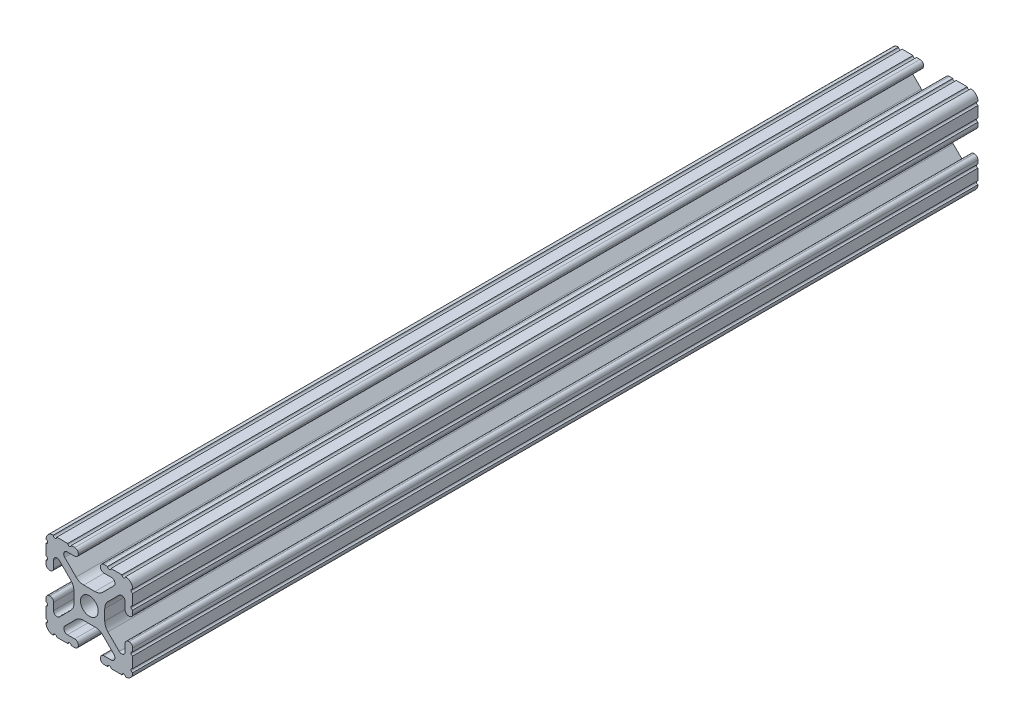
SolidWorks part; units mm, degrees
ref_plane "Front Plane" through (0, 0, 0) normal (0, 0, 1) x (1, 0, 0)
ref_plane "Top Plane" through (0, 0, 0) normal (0, 1, 0) x (1, 0, 0)
ref_plane "Right Plane" through (0, 0, 0) normal (1, 0, 0) x (0, 0, -1)
sketch "Sketch1" plane through (0, 0, 0) normal (0, 0, 1) x (1, 0, 0)
  line L88 (-7.1797, -8.6452) -> (-3.9523, -5.4237)
  line L89 (-1.7093, -4.4958) -> (1.7093, -4.4958)
  line L90 (3.9523, -5.4237) -> (7.1797, -8.6452)
  line L91 (6.4164, -10.4902) -> (4.2875, -10.4902)
  line L92 (3.2385, -11.5392) -> (3.2385, -11.651)
  line L93 (4.2875, -12.7) -> (5.3171, -12.7)
  line L94 (6.3331, -12.7) -> (9.5504, -12.7)
  line L95 (12.7, -9.5504) -> (12.7, -6.3331)
  line L96 (12.7, -5.3171) -> (12.7, -4.2875)
  line L97 (11.651, -3.2385) -> (11.5392, -3.2385)
  line L98 (10.4902, -4.2875) -> (10.4902, -6.4021)
  line L99 (8.7371, -7.1294) -> (5.441, -3.8408)
  line L100 (4.5085, -1.5932) -> (4.5085, 1.5932)
  line L101 (5.441, 3.8408) -> (8.7371, 7.1294)
  line L102 (10.4902, 6.4021) -> (10.4902, 4.2875)
  line L103 (11.5392, 3.2385) -> (11.651, 3.2385)
  line L104 (12.7, 4.2875) -> (12.7, 5.3171)
  line L105 (12.7, 6.3331) -> (12.7, 9.5504)
  line L106 (9.5504, 12.7) -> (6.3331, 12.7)
  line L107 (5.3171, 12.7) -> (4.2875, 12.7)
  line L108 (3.2385, 11.651) -> (3.2385, 11.5392)
  line L109 (4.2875, 10.4902) -> (6.4768, 10.4902)
  line L110 (7.207, 8.7244) -> (3.8983, 5.4232)
  line L111 (1.6558, 4.4958) -> (-1.6558, 4.4958)
  line L112 (-3.8983, 5.4232) -> (-7.207, 8.7244)
  line L113 (-6.4768, 10.4902) -> (-4.2875, 10.4902)
  line L114 (-3.2385, 11.5392) -> (-3.2385, 11.651)
  line L115 (-4.2875, 12.7) -> (-5.3171, 12.7)
  line L116 (-6.3331, 12.7) -> (-9.5504, 12.7)
  line L117 (-12.7, 9.5504) -> (-12.7, 6.3331)
  line L118 (-12.7, 5.3171) -> (-12.7, 4.2875)
  line L119 (-11.651, 3.2385) -> (-11.5392, 3.2385)
  line L120 (-10.4902, 4.2875) -> (-10.4902, 6.4021)
  line L121 (-8.7371, 7.1294) -> (-5.441, 3.8408)
  line L122 (-4.5085, 1.5932) -> (-4.5085, -1.5932)
  line L123 (-5.441, -3.8408) -> (-8.7371, -7.1294)
  line L124 (-10.4902, -6.4021) -> (-10.4902, -4.2875)
  line L125 (-11.5392, -3.2385) -> (-11.651, -3.2385)
  line L126 (-12.7, -4.2875) -> (-12.7, -5.3171)
  line L127 (-12.7, -6.3331) -> (-12.7, -9.5504)
  line L128 (-9.5504, -12.7) -> (-6.3331, -12.7)
  line L129 (-5.3171, -12.7) -> (-4.2875, -12.7)
  line L130 (-3.2385, -11.651) -> (-3.2385, -11.5392)
  line L131 (-4.2875, -10.4902) -> (-6.4164, -10.4902)
  circle A1 centre (0, 0) radius 2.6035
  arc A104 (-7.1797, -8.6452) -> (-6.4164, -10.4902) centre (-6.4164, -9.4098) ccw
  arc A105 (-1.7093, -4.4958) -> (-3.9523, -5.4237) centre (-1.7093, -7.6708) ccw
  arc A106 (3.9523, -5.4237) -> (1.7093, -4.4958) centre (1.7093, -7.6708) ccw
  arc A107 (6.4164, -10.4902) -> (7.1797, -8.6452) centre (6.4164, -9.4098) ccw
  arc A108 (4.2875, -10.4902) -> (3.2385, -11.5392) centre (4.2875, -11.5392) ccw
  arc A109 (3.2385, -11.651) -> (4.2875, -12.7) centre (4.2875, -11.651) ccw
  arc A110 (6.3331, -12.7) -> (5.3171, -12.7) centre (5.8251, -12.7) ccw
  arc A111 (10.5664, -12.6998) -> (9.5504, -12.7) centre (10.0584, -12.7) ccw
  arc A112 (10.5664, -12.6998) -> (12.6998, -10.5664) centre (10.5918, -10.5918) ccw
  arc A113 (12.7, -9.5504) -> (12.6998, -10.5664) centre (12.7, -10.0584) ccw
  arc A114 (12.7, -5.3171) -> (12.7, -6.3331) centre (12.7, -5.8251) ccw
  arc A115 (12.7, -4.2875) -> (11.651, -3.2385) centre (11.651, -4.2875) ccw
  arc A116 (11.5392, -3.2385) -> (10.4902, -4.2875) centre (11.5392, -4.2875) ccw
  arc A117 (8.7371, -7.1294) -> (10.4902, -6.4021) centre (9.4628, -6.4021) ccw
  arc A118 (4.5085, -1.5932) -> (5.441, -3.8408) centre (7.6835, -1.5932) ccw
  arc A119 (5.441, 3.8408) -> (4.5085, 1.5932) centre (7.6835, 1.5932) ccw
  arc A120 (10.4902, 6.4021) -> (8.7371, 7.1294) centre (9.4628, 6.4021) ccw
  arc A121 (10.4902, 4.2875) -> (11.5392, 3.2385) centre (11.5392, 4.2875) ccw
  arc A122 (11.651, 3.2385) -> (12.7, 4.2875) centre (11.651, 4.2875) ccw
  arc A123 (12.7, 6.3331) -> (12.7, 5.3171) centre (12.7, 5.8251) ccw
  arc A124 (12.6998, 10.5664) -> (12.7, 9.5504) centre (12.7, 10.0584) ccw
  arc A125 (12.6998, 10.5664) -> (10.5664, 12.6998) centre (10.5918, 10.5918) ccw
  arc A126 (9.5504, 12.7) -> (10.5664, 12.6998) centre (10.0584, 12.7) ccw
  arc A127 (5.3171, 12.7) -> (6.3331, 12.7) centre (5.8251, 12.7) ccw
  arc A128 (4.2875, 12.7) -> (3.2385, 11.651) centre (4.2875, 11.651) ccw
  arc A129 (3.2385, 11.5392) -> (4.2875, 10.4902) centre (4.2875, 11.5392) ccw
  arc A130 (7.207, 8.7244) -> (6.4768, 10.4902) centre (6.4768, 9.4563) ccw
  arc A131 (1.6558, 4.4958) -> (3.8983, 5.4232) centre (1.6558, 7.6708) ccw
  arc A132 (-3.8983, 5.4232) -> (-1.6558, 4.4958) centre (-1.6558, 7.6708) ccw
  arc A133 (-6.4768, 10.4902) -> (-7.207, 8.7244) centre (-6.4768, 9.4563) ccw
  arc A134 (-4.2875, 10.4902) -> (-3.2385, 11.5392) centre (-4.2875, 11.5392) ccw
  arc A135 (-3.2385, 11.651) -> (-4.2875, 12.7) centre (-4.2875, 11.651) ccw
  arc A136 (-6.3331, 12.7) -> (-5.3171, 12.7) centre (-5.8251, 12.7) ccw
  arc A137 (-10.5664, 12.6998) -> (-9.5504, 12.7) centre (-10.0584, 12.7) ccw
  arc A138 (-10.5664, 12.6998) -> (-12.6998, 10.5664) centre (-10.5918, 10.5918) ccw
  arc A139 (-12.7, 9.5504) -> (-12.6998, 10.5664) centre (-12.7, 10.0584) ccw
  arc A140 (-12.7, 5.3171) -> (-12.7, 6.3331) centre (-12.7, 5.8251) ccw
  arc A141 (-12.7, 4.2875) -> (-11.651, 3.2385) centre (-11.651, 4.2875) ccw
  arc A142 (-11.5392, 3.2385) -> (-10.4902, 4.2875) centre (-11.5392, 4.2875) ccw
  arc A143 (-8.7371, 7.1294) -> (-10.4902, 6.4021) centre (-9.4628, 6.4021) ccw
  arc A144 (-4.5085, 1.5932) -> (-5.441, 3.8408) centre (-7.6835, 1.5932) ccw
  arc A145 (-5.441, -3.8408) -> (-4.5085, -1.5932) centre (-7.6835, -1.5932) ccw
  arc A146 (-10.4902, -6.4021) -> (-8.7371, -7.1294) centre (-9.4628, -6.4021) ccw
  arc A147 (-10.4902, -4.2875) -> (-11.5392, -3.2385) centre (-11.5392, -4.2875) ccw
  arc A148 (-11.651, -3.2385) -> (-12.7, -4.2875) centre (-11.651, -4.2875) ccw
  arc A149 (-12.7, -6.3331) -> (-12.7, -5.3171) centre (-12.7, -5.8251) ccw
  arc A150 (-12.6998, -10.5664) -> (-12.7, -9.5504) centre (-12.7, -10.0584) ccw
  arc A151 (-12.6998, -10.5664) -> (-10.5664, -12.6998) centre (-10.5918, -10.5918) ccw
  arc A152 (-9.5504, -12.7) -> (-10.5664, -12.6998) centre (-10.0584, -12.7) ccw
  arc A153 (-5.3171, -12.7) -> (-6.3331, -12.7) centre (-5.8251, -12.7) ccw
  arc A154 (-4.2875, -12.7) -> (-3.2385, -11.651) centre (-4.2875, -11.651) ccw
  arc A155 (-3.2385, -11.5392) -> (-4.2875, -10.4902) centre (-4.2875, -11.5392) ccw
extrude "Boss-Extrude1" add sketch "Sketch1" along normal mid plane 247.65
